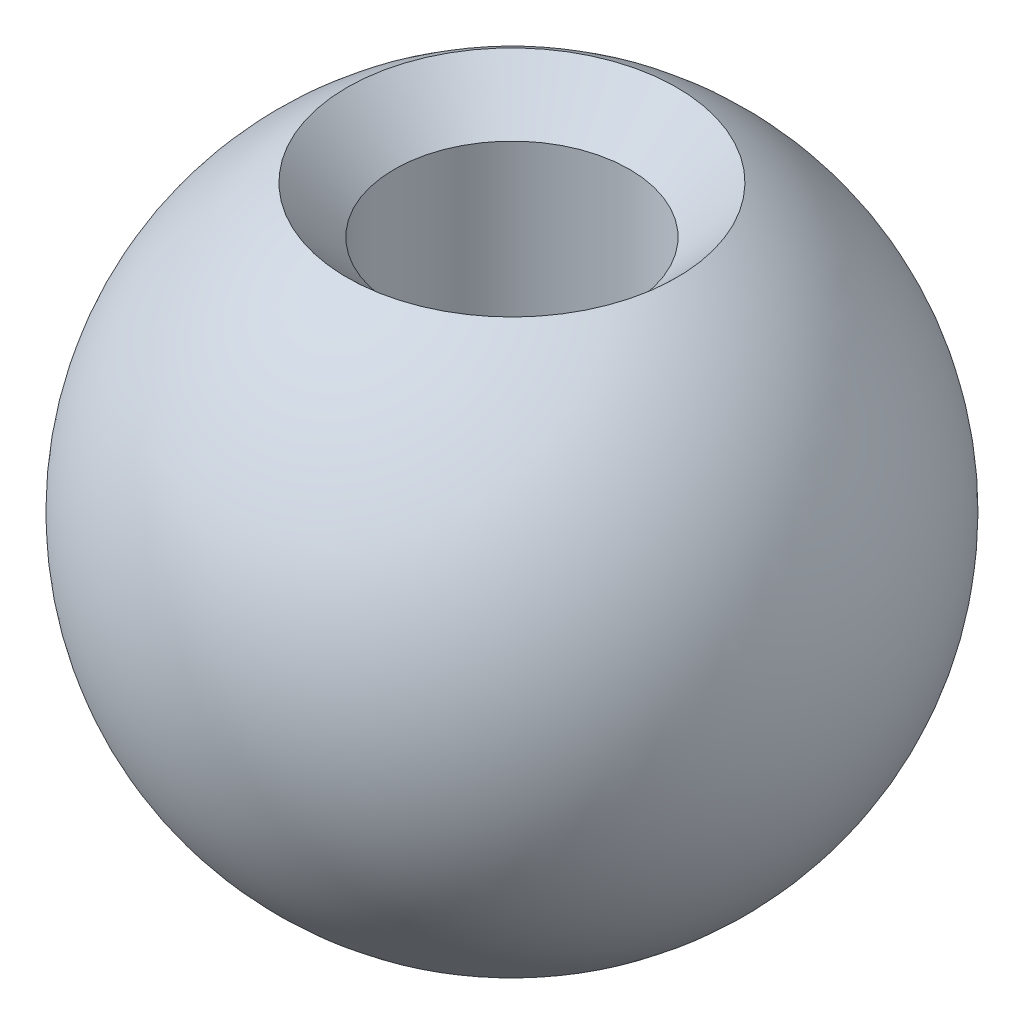
SolidWorks part; units mm, degrees
material "Chrome Stainless Steel"
ref_plane "Front Plane" through (0, 0, 0) normal (0, 0, 1) x (1, 0, 0)
ref_plane "Top Plane" through (0, 0, 0) normal (0, 1, 0) x (1, 0, 0)
ref_plane "Right Plane" through (0, 0, 0) normal (1, 0, 0) x (0, 0, -1)
sketch "Sketch1" plane through (0, 0, 0) normal (0, 0, 1) x (1, 0, 0)
  line L0 (0, 9.6174) -> (0, -9.6174) construction
  line L1 (1.9812, 4.0149) -> (1.9812, -5.191)
  line L2 (1.9812, 4.0149) -> (2.7781, 4.8119)
  line L3 (0, 0) -> (10.1073, 0) construction
  arc A0 (2.7781, 4.8119) -> (1.9812, -5.191) centre (0, 0) cw
  dimension "D1" = 5.5562
  dimension "D2" = 3.9624
  dimension "D3" = 45
  dimension "D4" = 5.5562
revolve "Revolve2" add sketch "Sketch1" angle 360 about L0
